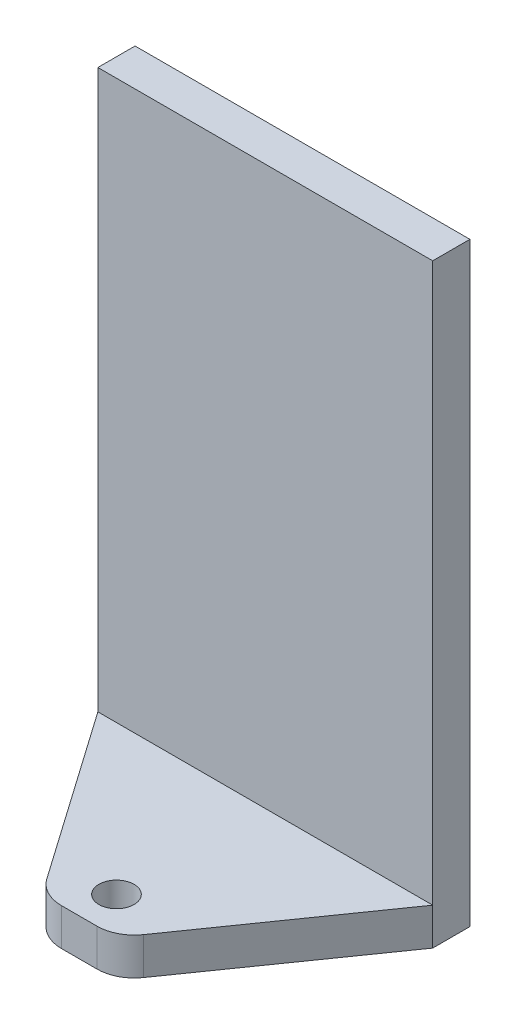
SolidWorks part; units mm, degrees
material "PLA White"
ref_plane "Front" through (0, 0, 0) normal (0, 0, 1) x (1, 0, 0)
ref_plane "Top" through (0, 0, 0) normal (0, 1, 0) x (1, 0, 0)
ref_plane "Right" through (0, 0, 0) normal (1, 0, 0) x (0, 0, -1)
sketch "Sketch1" plane through (0, 0, 0) normal (0, 0, 1) x (1, 0, 0)
  line L1 (-28.575, -50.8) -> (28.575, -50.8)
  line L2 (-28.575, -50.8) -> (-28.575, 50.8)
  line L3 (-28.575, 50.8) -> (28.575, 50.8)
  line L4 (28.575, -50.8) -> (28.575, 50.8)
  line L5 (-28.575, -50.8) -> (28.575, 50.8) construction
  line L6 (-28.575, 50.8) -> (28.575, -50.8) construction
  point P0 (0, 0)
  dimension "D1" = 57.15
  dimension "D2" = 101.6
extrude "Boss-Extrude1" add sketch "Sketch1" along normal mid plane 6.35
sketch "Sketch2" plane through (0, -50.8, 0) normal (0, -1, 0) x (1, 0, 0)
  line L0 (-28.575, 3.175) -> (28.575, 3.175) construction
  line L1 (-28.575, -3.175) -> (28.575, -3.175)
  line L2 (-28.575, -3.175) -> (-28.575, 53.975)
  line L3 (-28.575, 53.975) -> (28.575, 53.975)
  line L4 (28.575, -3.175) -> (28.575, 53.975)
  dimension "D1" = 50.8
extrude "Boss-Extrude2" add sketch "Sketch2" against normal blind 6.35
sketch "Sketch4" plane through (0, -44.45, 0) normal (0, 1, 0) x (1, 0, 0)
  line L0 (-28.575, -53.975) -> (-28.575, -3.175) construction
  line L1 (28.575, -53.975) -> (-28.575, -53.975) construction
  circle A0 centre (0, -28.575) radius 3
  point P4 (-28.575, -28.575)
  point P7 (0, -53.975)
  dimension "D1" = 6
extrude "Cut-Extrude2" cut sketch "Sketch4" against normal through all
sketch "Sketch5" plane through (0, -44.45, 0) normal (0, 1, 0) x (1, 0, 0)
  line L0 (-28.575, -3.175) -> (-6.35, -34.925)
  line L1 (-6.35, -34.925) -> (6.35, -34.925)
  line L2 (6.35, -34.925) -> (28.575, -3.175)
  line L3 (28.575, -3.175) -> (28.575, -53.975)
  line L4 (28.575, -53.975) -> (-28.575, -53.975)
  line L5 (-28.575, -53.975) -> (-28.575, -3.175)
  line L6 (0, -34.925) -> (0, -53.975) construction
  circle A0 centre (0, -28.575) radius 3 construction
  dimension "D1" = 6.35
  dimension "D2" = 12.7
extrude "Cut-Extrude3" cut sketch "Sketch5" against normal through all
fillet "Fillet1" radius 6.35 2 edges at (6.35, -47.625, 34.925) (-6.35, -47.625, 34.925)
